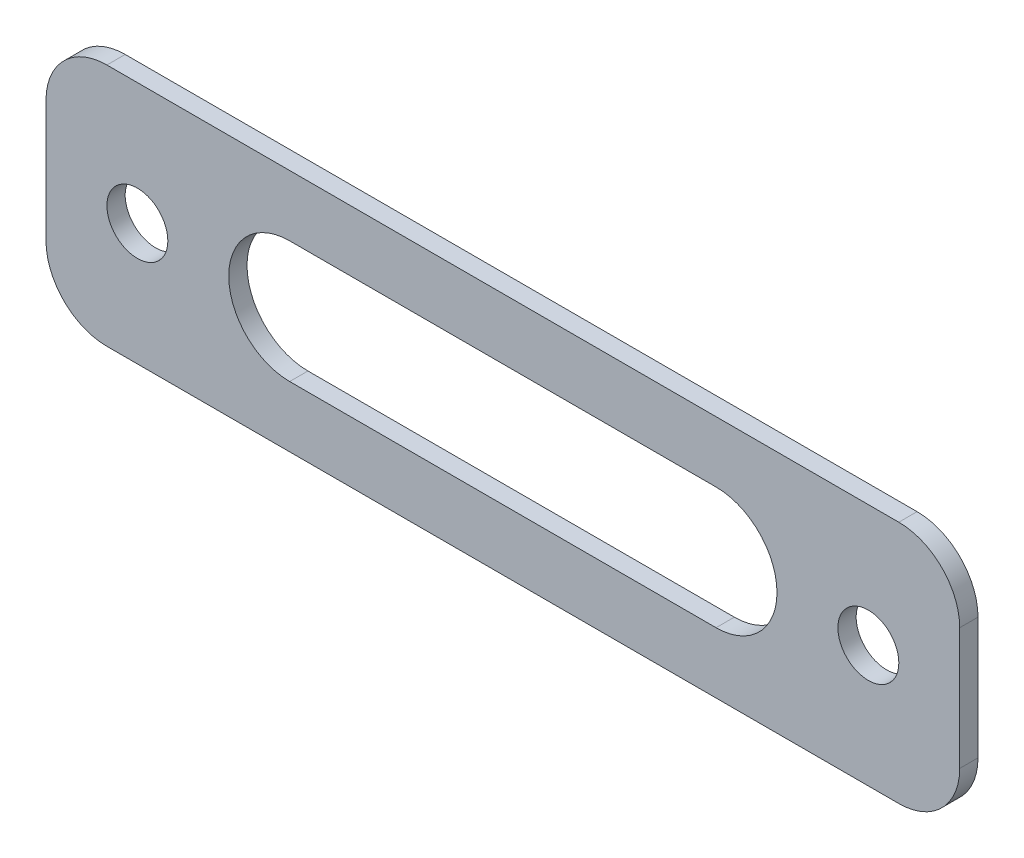
SolidWorks part; units mm, degrees
ref_plane "Front" through (0, 0, 0) normal (0, 0, 1) x (1, 0, 0)
ref_plane "Top" through (0, 0, 0) normal (0, 1, 0) x (1, 0, 0)
ref_plane "Right" through (0, 0, 0) normal (1, 0, 0) x (0, 0, -1)
sketch "Sketch1" plane through (0, 0, 0) normal (0, 0, 1) x (1, 0, 0)
  line L0 (-38.1, 0) -> (38.1, 0) construction
  line L1 (-47.625, 12.7) -> (47.625, 12.7)
  line L2 (-47.625, 12.7) -> (-47.625, -12.7)
  line L3 (-47.625, -12.7) -> (47.625, -12.7)
  line L4 (47.625, 12.7) -> (47.625, -12.7)
  line L5 (-47.625, 12.7) -> (47.625, -12.7) construction
  line L6 (-47.625, -12.7) -> (47.625, 12.7) construction
  circle A0 centre (-38.1, 0) radius 3.175
  circle A1 centre (38.1, 0) radius 3.175
  point P0 (0, 0)
  dimension "D3" = 6.35
  dimension "D1" = 95.25
  dimension "D2" = 25.4
  dimension "D4" = 76.2
extrude "Boss-Extrude1" add sketch "Sketch1" along normal blind 1.905
sketch "Sketch2" plane through (0, 0, 1.905) normal (0, 0, 1) x (1, 0, 0)
  line L0 (-22.225, 0) -> (22.225, 0) construction
  line L1 (-22.225, 6.35) -> (22.225, 6.35)
  line L2 (-22.225, -6.35) -> (22.225, -6.35)
  arc A0 (-22.225, 6.35) -> (-22.225, -6.35) centre (-22.225, 0) ccw
  arc A1 (22.225, -6.35) -> (22.225, 6.35) centre (22.225, 0) ccw
  point P3 (0, 0)
  dimension "D1" = 12.7
  dimension "D2" = 44.45
extrude "Cut-Extrude1" cut sketch "Sketch2" against normal through all
fillet "Fillet1" radius 6.35 4 edges at (47.625, -12.7, 0.9525) (47.625, 12.7, 0.9525) (-47.625, -12.7, 0.9525) (-47.625, 12.7, 0.9525)
